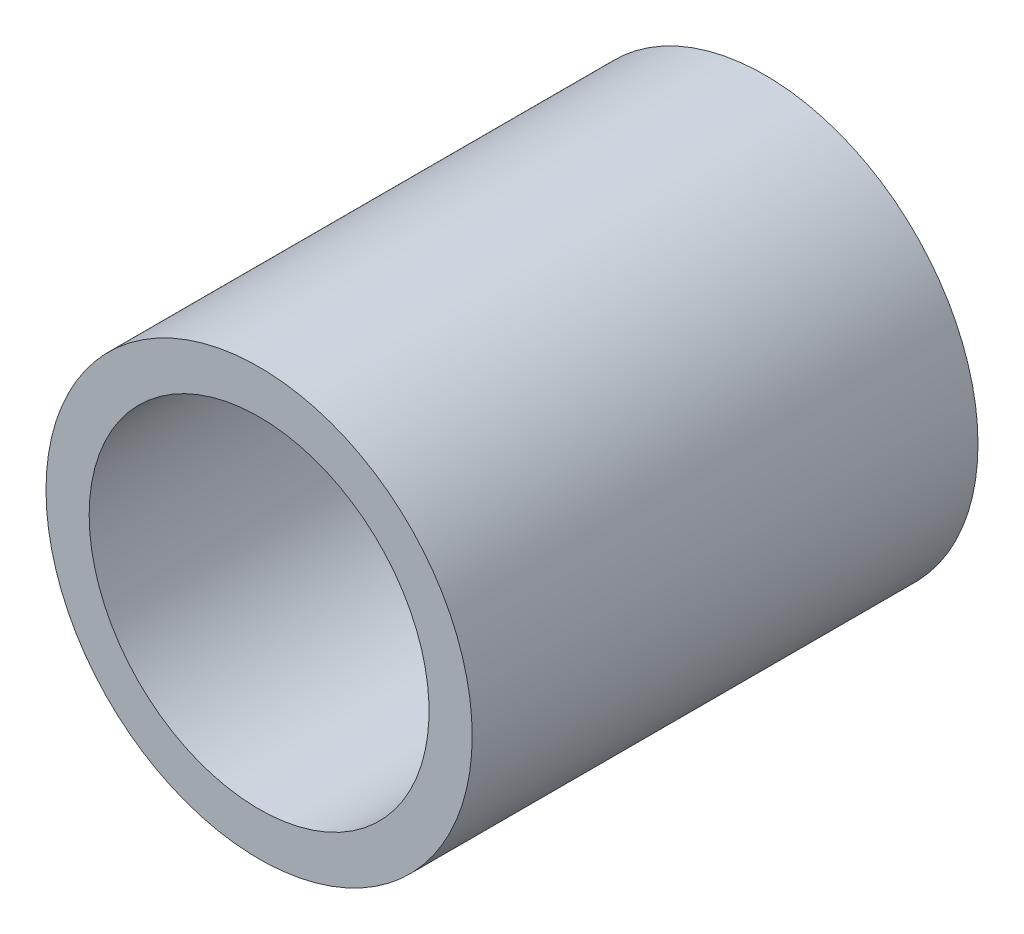
SolidWorks part; units mm, degrees
material "841 Oilite Bronze"
ref_plane "Front Plane" through (0, 0, 0) normal (0, 0, 1) x (1, 0, 0)
ref_plane "Top Plane" through (0, 0, 0) normal (0, 1, 0) x (1, 0, 0)
ref_plane "Right Plane" through (0, 0, 0) normal (1, 0, 0) x (0, 0, -1)
sketch "Sketch1" plane through (0, 0, 0) normal (0, 0, 1) x (1, 0, 0)
  circle A0 centre (0, 0) radius 4.0132
  circle A1 centre (0, 0) radius 3.2004
  dimension "OD" = 8.0264
  dimension "ID" = 6.4008
sketch "Sketch2" plane through (0, 0, 0) normal (1, 0, 0) x (0, 0, -1)
  line L2 (4.7625, 0) -> (-4.7625, 0) construction
  line L4 (-4.7625, -4.0132) -> (-4.7625, 4.0132) construction
  line L5 (-4.7625, -3.2004) -> (4.7625, -3.2004)
  line L6 (4.7625, 3.2004) -> (-4.7625, 3.2004)
  line L7 (4.7625, -4.0132) -> (4.7625, 4.0132) construction
  line L8 (-4.7625, 4.0132) -> (4.7625, 4.0132) construction
  line L9 (-4.7625, -4.0132) -> (4.7625, -4.0132) construction
  line L10 (0, 4.0132) -> (0, -4.0132) construction
  line L11 (0, 3.2004) -> (0, -3.2004) construction
  point P4 (0, -3.2004)
  point P7 (0, 3.2004)
  point P8 (0, 0)
  point P12 (-4.7625, 0)
  point P15 (4.7625, 0)
  point P16 (0, -4.0132)
  point P17 (0, 4.0132)
  dimension "Length" = 9.525
sketch "Sketch5" plane through (0, 0, 0) normal (0, 0, 1) x (1, 0, 0)
  circle A1 centre (0, 0) radius 3.2004
  circle A2 centre (0, 0) radius 3.2004
  circle A3 centre (0, 0) radius 4.0132
  circle A4 centre (0, 0) radius 4.0132
  dimension "D1" = 0
  dimension "D2" = 0
extrude "Boss-Extrude1" add sketch "Sketch5" along normal mid plane 9.525
equation "\"D1@Boss-Extrude1\" = \"Length@Sketch2\""
